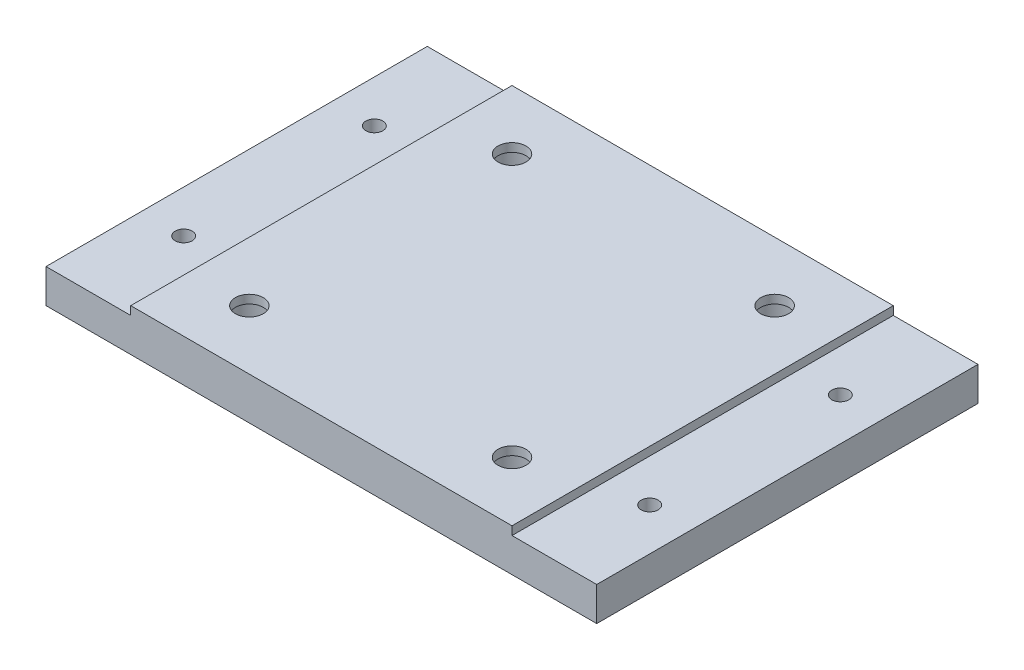
SolidWorks part; units mm, degrees
material "ABS"
ref_plane "Front Plane" through (0, 0, 0) normal (0, 0, 1) x (1, 0, 0)
ref_plane "Top Plane" through (0, 0, 0) normal (0, 1, 0) x (1, 0, 0)
ref_plane "Right Plane" through (0, 0, 0) normal (1, 0, 0) x (0, 0, -1)
sketch "Sketch1" plane through (0, 0, 0) normal (0, 1, 0) x (1, 0, 0)
  line L0 (-22.5, -22.5) -> (-32.5, -22.5)
  line L1 (-32.5, -22.5) -> (-32.5, 22.5)
  line L2 (-22.5, 22.5) -> (22.5, 22.5)
  line L4 (22.5, -22.5) -> (-22.5, -22.5)
  line L6 (-32.5, 22.5) -> (-22.5, 22.5)
  line L7 (22.5, 22.5) -> (32.5, 22.5)
  line L8 (32.5, 22.5) -> (32.5, -22.5)
  line L9 (32.5, -22.5) -> (22.5, -22.5)
  circle A0 centre (-15.5, 15.5) radius 3
  circle A1 centre (15.5, 15.5) radius 3
  circle A2 centre (15.5, -15.5) radius 3
  circle A3 centre (-15.5, -15.5) radius 3
  circle A4 centre (-27.5, 11.25) radius 1
  circle A5 centre (-27.5, -11.25) radius 1
  circle A6 centre (27.5, 11.25) radius 1
  circle A7 centre (27.5, -11.25) radius 1
extrude "Boss-Extrude1" add sketch "Sketch1" along normal blind 4
sketch "Sketch2" plane through (0, 4, 0) normal (0, 1, 0) x (1, 0, 0)
  line L6 (32.5, 22.5) -> (-32.5, 22.5) construction
  line L7 (-22.5, 22.5) -> (22.5, 22.5)
  line L8 (22.5, 22.5) -> (22.5, -22.5)
  line L9 (-32.5, -22.5) -> (32.5, -22.5) construction
  line L10 (22.5, -22.5) -> (-22.5, -22.5)
  line L11 (-22.5, -22.5) -> (-22.5, 22.5)
  circle A0 centre (-15.5, -15.5) radius 1.65
  circle A1 centre (15.5, -15.5) radius 1.65
  circle A2 centre (15.5, 15.5) radius 1.65
  circle A3 centre (-15.5, 15.5) radius 1.65
extrude "Boss-Extrude2" add sketch "Sketch2" along normal blind 1
